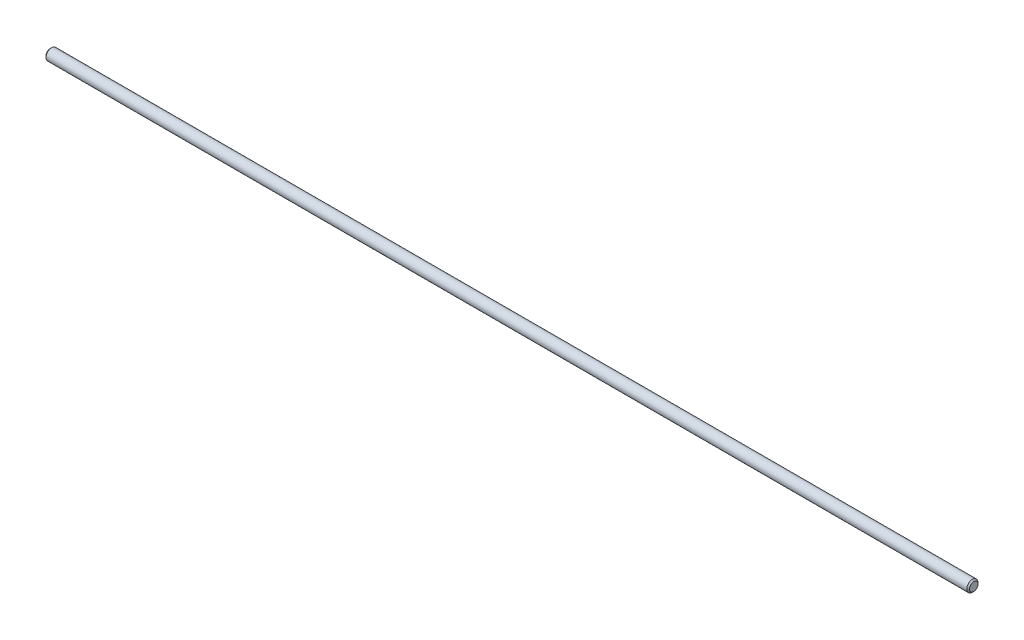
SolidWorks part; units mm, degrees
ref_plane "Front Plane" through (0, 0, 0) normal (0, 0, 1) x (1, 0, 0)
ref_plane "Top Plane" through (0, 0, 0) normal (0, 1, 0) x (1, 0, 0)
ref_plane "Right Plane" through (0, 0, 0) normal (1, 0, 0) x (0, 0, -1)
sketch "Sketch1" plane through (0, 0, 0) normal (0, 0, 1) x (1, 0, 0)
  line L0 (-82.175, 0) -> (82.175, 0) construction
  line L1 (82.175, 1) -> (82.175, -1) construction
  line L2 (-82.175, 1) -> (-82.175, -1) construction
  point P6 (80.775, -1)
  dimension "D1" = 1.4
  dimension "Thread Diameter" = 2
  dimension "Length" = 164.35
sketch "Sketch2" plane through (0, 0, 0) normal (1, 0, 0) x (0, 0, -1)
  circle A0 centre (0, 0) radius 1
extrude "Boss-Extrude1" add sketch "Sketch2" against normal up to vertex (82.175 mm away) and the other way up to vertex (82.175 mm away) up to point (-82.175, 0, 0) other way up to point (82.175, 0, 0)
sketch "Sketch3" plane through (82.175, 0, 0) normal (1, 0, 0) x (0, 0, -1)
  circle A1 centre (0, 0) radius 1
  circle A2 centre (0, 0) radius 1
  dimension "D1" = 0
curve "Helix/Spiral1" pitch 0.4 height 101 turns 252.5
sketch "Sketch4" plane through (0, 0, 0) normal (0, 0, 1) x (1, 0, 0)
  line L1 (82.1464, 1.0495) -> (82.5464, 1.0495) construction
  line L2 (82.1464, 1.0495) -> (82.3464, 0.7031) construction
  line L3 (82.3464, 0.7031) -> (82.5464, 1.0495) construction
  line L4 (82.3464, 1.0495) -> (82.3464, 1) construction
  line L5 (82.3464, 0.7031) -> (82.3464, 0.7526) construction
  line L6 (82.3179, 0.7526) -> (82.375, 0.7526) construction
  line L7 (82.175, 1) -> (82.5179, 1) construction
  line L8 (82.175, 1) -> (82.3179, 0.7526)
  line L9 (82.3179, 0.7526) -> (82.375, 0.7526)
  line L10 (82.375, 0.7526) -> (82.5179, 1)
  line L11 (82.5179, 1) -> (82.175, 1)
  dimension "Pitch" = 0.4
  dimension "D2" = 0.0571
sketch "Sketch5" plane through (82.175, 0, 0) normal (1, 0, 0) x (0, 0, -1)
  circle A0 centre (0, 0) radius 0.7526
extrude "Cut-Extrude1" cut sketch "Sketch5" against normal through all draft 45 flip side to cut
mirror "Mirror1" about plane through (0, 0, 0) normal (1, 0, 0) of "Cut-Extrude1"
equation "\"D2@Sketch4\" = \"Pitch@Sketch4\"/7"
